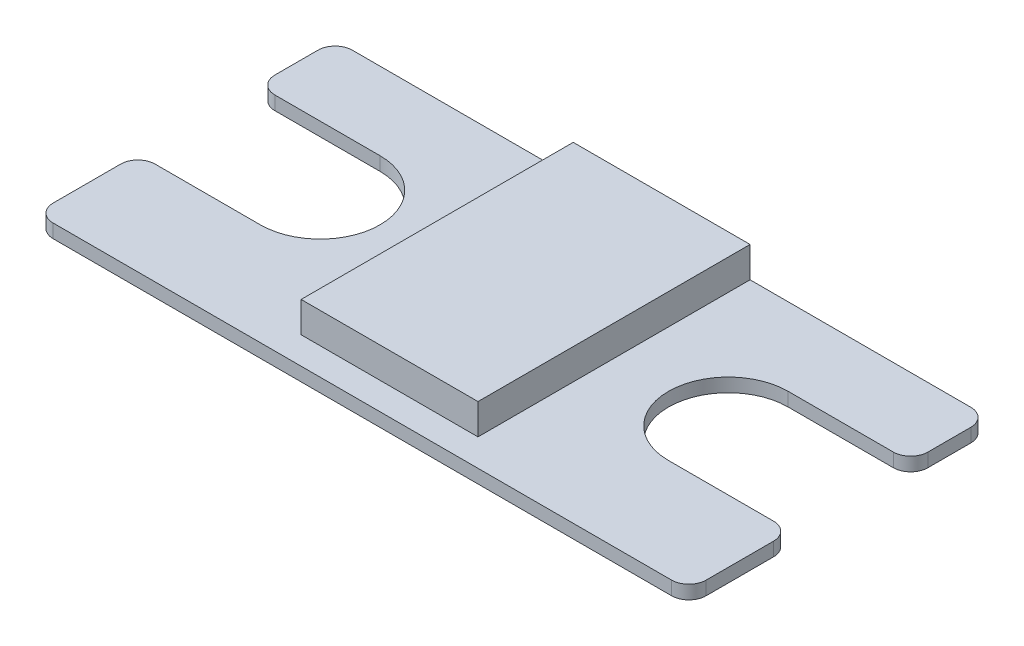
SolidWorks part; units mm, degrees
ref_plane "Front Plane" through (0, 0, 0) normal (0, 0, 1) x (1, 0, 0)
ref_plane "Top Plane" through (0, 0, 0) normal (0, 1, 0) x (1, 0, 0)
ref_plane "Right Plane" through (0, 0, 0) normal (1, 0, 0) x (0, 0, -1)
sketch "Sketch1" plane through (0, 0, 0) normal (0, 1, 0) x (1, 0, 0)
  line L0 (0, 0) -> (0, 7.5)
  line L1 (0, 7.5) -> (9, 7.5)
  line L3 (9, 16.3) -> (0, 16.3)
  line L4 (0, 16.3) -> (0, 22)
  line L5 (0, 22) -> (48, 22)
  line L6 (48, 22) -> (48, 16.3)
  line L7 (48, 16.3) -> (39, 16.3)
  line L9 (39, 7.5) -> (48, 7.5)
  line L10 (48, 7.5) -> (48, 0)
  line L11 (48, 0) -> (0, 0)
  arc A0 (9, 16.3) -> (9, 7.5) centre (9, 11.9) cw
  arc A1 (39, 7.5) -> (39, 16.3) centre (39, 11.9) cw
  dimension "D1" = 7.5
  dimension "D2" = 9
  dimension "D3" = 48
  dimension "D4" = 22
  dimension "D5" = 5.7
extrude "Boss-Extrude1" add sketch "Sketch1" along normal blind 1
fillet "Fillet1" radius 1.27 8 edges at (48, 0.5, 0) (48, 0.5, -7.5) (48, 0.5, -16.3) (48, 0.5, -22) (0, 0.5, -22) (0, 0.5, -16.3) (0, 0.5, -7.5) (0, 0.5, 0)
sketch "Sketch2" plane through (0, 1, 0) normal (0, 1, 0) x (1, 0, 0)
  line L0 (46.73, 22) -> (1.27, 22) construction
  line L1 (17.5, 22) -> (30.5, 22)
  line L2 (17.5, 22) -> (17.5, 2)
  line L3 (17.5, 2) -> (30.5, 2)
  line L4 (30.5, 22) -> (30.5, 2)
  line L5 (1.27, 0) -> (46.73, 0) construction
  point P8 (24, 0)
  point P9 (24, 2)
  dimension "D1" = 13
  dimension "D2" = 20
extrude "Boss-Extrude2" add sketch "Sketch2" along normal blind 2.25
